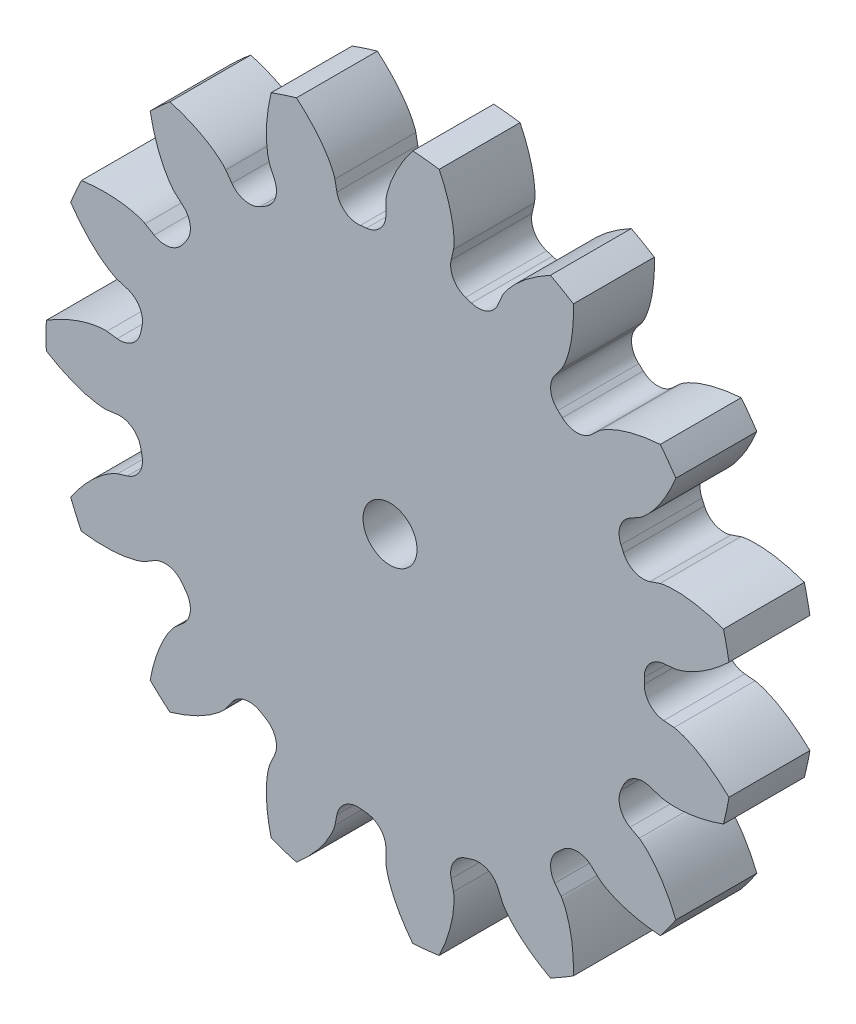
SolidWorks part; units mm, degrees
material "Acrylic (Medium-high impact)"
ref_plane "Front Plane" through (0, 0, 0) normal (0, 0, 1) x (1, 0, 0)
ref_plane "Top Plane" through (0, 0, 0) normal (0, 1, 0) x (1, 0, 0)
ref_plane "Right Plane" through (0, 0, 0) normal (1, 0, 0) x (0, 0, -1)
sketch "Model" plane through (0, 0, 0) normal (0, 0, 1) x (1, 0, 0)
  line L40 (-34.0113, -11.6188) -> (-34.7748, -11.5274)
  line L41 (-34.7748, -16.5738) -> (-34.0113, -16.4825)
  line L42 (-33.2515, -20.0567) -> (-33.9862, -20.2838)
  line L43 (-31.9337, -24.8939) -> (-31.2733, -24.4999)
  line L44 (-29.1255, -27.4561) -> (-29.7043, -27.9624)
  line L45 (-25.9541, -31.3391) -> (-25.5111, -30.7105)
  line L46 (-22.3465, -32.5376) -> (-22.6694, -33.2355)
  line L47 (-17.87, -34.7949) -> (-17.7209, -34.0405)
  line L48 (-14.0869, -34.4225) -> (-14.0979, -35.1914)
  line L49 (-9.0792, -34.6639) -> (-9.2499, -33.9141)
  line L50 (-5.7746, -32.7849) -> (-5.472, -33.4918)
  line L51 (-1.1017, -30.9686) -> (-1.5626, -30.3531)
  line L52 (1.153, -27.908) -> (1.717, -28.4307)
  line L53 (4.6832, -24.3481) -> (4.0117, -23.9732)
  line L54 (5.498, -20.635) -> (6.2259, -20.8832)
  line L55 (7.2751, -15.9471) -> (6.5092, -15.8777)
  line L56 (6.5092, -12.2236) -> (7.2751, -12.1542)
  line L57 (6.2259, -7.2181) -> (5.498, -7.4662)
  line L58 (4.0117, -4.128) -> (4.6832, -3.7532)
  line L59 (1.717, 0.3295) -> (1.153, -0.1933)
  line L60 (-1.5626, 2.2518) -> (-1.1017, 2.8674)
  line L61 (-5.472, 5.3906) -> (-5.7746, 4.6836)
  line L62 (-9.2499, 5.8128) -> (-9.0792, 6.5626)
  line L63 (-14.0979, 7.0901) -> (-14.0869, 6.3212)
  line L64 (-17.7209, 5.9392) -> (-17.87, 6.6936)
  line L65 (-22.6694, 5.1342) -> (-22.3465, 4.4363)
  line L66 (-25.5111, 2.6092) -> (-25.9541, 3.2378)
  line L67 (-29.7043, -0.1389) -> (-29.1255, -0.6452)
  line L68 (-31.2733, -3.6014) -> (-31.9337, -3.2074)
  line L69 (-33.9862, -7.8175) -> (-33.2515, -8.0446)
  arc A81 (-32.1716, -9.91) -> (-32.2659, -10.3539) centre (-13.7828, -14.0506) ccw
  arc A82 (-34.0113, -11.6188) -> (-32.2659, -10.3539) centre (-33.8226, -10.0426) ccw
  arc A83 (-39.2638, -13.0663) -> (-39.2638, -15.035) centre (-13.7828, -14.0506) ccw
  arc A84 (-32.2659, -17.7474) -> (-34.0113, -16.4825) centre (-33.8226, -18.0587) ccw
  arc A85 (-32.2659, -17.7474) -> (-32.1716, -18.1913) centre (-13.7828, -14.0506) ccw
  arc A86 (-33.2515, -20.0567) -> (-32.1716, -18.1913) centre (-33.7203, -18.54) ccw
  arc A87 (-37.4612, -23.5154) -> (-36.6605, -25.3139) centre (-13.7828, -14.0506) ccw
  arc A88 (-29.1644, -24.9455) -> (-31.2733, -24.4999) centre (-30.4599, -25.8631) ccw
  arc A89 (-29.1644, -24.9455) -> (-28.8976, -25.3127) centre (-13.7828, -14.0506) ccw
  arc A90 (-29.1255, -27.4561) -> (-28.8976, -25.3127) centre (-30.1706, -26.2612) ccw
  arc A91 (-31.5644, -32.328) -> (-30.1014, -33.6454) centre (-13.7828, -14.0506) ccw
  arc A92 (-23.4032, -30.2599) -> (-25.5111, -30.7105) centre (-24.2135, -31.625) ccw
  arc A93 (-23.4032, -30.2599) -> (-23.0102, -30.4868) centre (-13.7828, -14.0506) ccw
  arc A94 (-22.3465, -32.5376) -> (-23.0102, -30.4868) centre (-23.7874, -31.8711) ccw
  arc A95 (-22.593, -37.9803) -> (-20.7207, -38.5887) centre (-13.7828, -14.0506) ccw
  arc A96 (-15.9786, -32.7715) -> (-17.7209, -34.0405) centre (-16.1635, -34.3482) ccw
  arc A97 (-15.9786, -32.7715) -> (-15.5273, -32.8189) centre (-13.7828, -14.0506) ccw
  arc A98 (-14.0869, -34.4225) -> (-15.5273, -32.8189) centre (-15.6742, -34.3996) ccw
  arc A99 (-12.0983, -39.4949) -> (-10.1404, -39.2891) centre (-13.7828, -14.0506) ccw
  arc A100 (-8.1743, -32.0461) -> (-9.2499, -33.9141) centre (-7.702, -33.5617) ccw
  arc A101 (-8.1743, -32.0461) -> (-7.7427, -31.9059) centre (-13.7828, -14.0506) ccw
  arc A102 (-5.7746, -32.7849) -> (-7.7427, -31.9059) centre (-7.234, -33.4097) ccw
  arc A103 (-1.8948, -36.61) -> (-0.1898, -35.6257) centre (-13.7828, -14.0506) ccw
  arc A104 (-1.3398, -28.2091) -> (-1.5626, -30.3531) centre (-0.2918, -29.4016) ccw
  arc A105 (-1.3398, -28.2091) -> (-1.0025, -27.9055) centre (-13.7828, -14.0506) ccw
  arc A106 (1.153, -27.908) -> (-1.0025, -27.9055) centre (0.0739, -29.0723) ccw
  arc A107 (6.2532, -29.8243) -> (7.4103, -28.2316) centre (-13.7828, -14.0506) ccw
  arc A108 (3.3433, -21.924) -> (4.0117, -23.9732) centre (4.7856, -22.5871) ccw
  arc A109 (3.3433, -21.924) -> (3.5278, -21.5094) centre (-13.7828, -14.0506) ccw
  arc A110 (5.498, -20.635) -> (3.5278, -21.5094) centre (4.9858, -22.1376) ccw
  arc A111 (10.9367, -20.3113) -> (11.346, -18.3856) centre (-13.7828, -14.0506) ccw
  arc A112 (5.065, -14.2775) -> (6.5092, -15.8777) centre (6.6524, -14.2967) ccw
  arc A113 (5.065, -14.2775) -> (5.065, -13.8237) centre (-13.7828, -14.0506) ccw
  arc A114 (6.5092, -12.2236) -> (5.065, -13.8237) centre (6.6524, -13.8046) ccw
  arc A115 (11.346, -9.7157) -> (10.9367, -7.79) centre (-13.7828, -14.0506) ccw
  arc A116 (3.5278, -6.5918) -> (5.498, -7.4662) centre (4.9858, -5.9636) ccw
  arc A117 (3.5278, -6.5918) -> (3.3433, -6.1772) centre (-13.7828, -14.0506) ccw
  arc A118 (4.0117, -4.128) -> (3.3433, -6.1772) centre (4.7856, -5.5141) ccw
  arc A119 (7.4103, 0.1304) -> (6.2532, 1.7231) centre (-13.7828, -14.0506) ccw
  arc A120 (-1.0025, -0.1958) -> (1.153, -0.1933) centre (0.0739, 0.9711) ccw
  arc A121 (-1.0025, -0.1958) -> (-1.3398, 0.1079) centre (-13.7828, -14.0506) ccw
  arc A122 (-1.5626, 2.2518) -> (-1.3398, 0.1079) centre (-0.2918, 1.3003) ccw
  arc A123 (-0.1898, 7.5244) -> (-1.8948, 8.5087) centre (-13.7828, -14.0506) ccw
  arc A124 (-7.7427, 3.8046) -> (-5.7746, 4.6836) centre (-7.234, 5.3084) ccw
  arc A125 (-7.7427, 3.8046) -> (-8.1743, 3.9448) centre (-13.7828, -14.0506) ccw
  arc A126 (-9.2499, 5.8128) -> (-8.1743, 3.9448) centre (-7.702, 5.4604) ccw
  arc A127 (-10.1404, 11.1879) -> (-12.0983, 11.3937) centre (-13.7828, -14.0506) ccw
  arc A128 (-15.5273, 4.7177) -> (-14.0869, 6.3212) centre (-15.6742, 6.2984) ccw
  arc A129 (-15.5273, 4.7177) -> (-15.9786, 4.6702) centre (-13.7828, -14.0506) ccw
  arc A130 (-17.7209, 5.9392) -> (-15.9786, 4.6702) centre (-16.1635, 6.2469) ccw
  arc A131 (-20.7207, 10.4874) -> (-22.593, 9.8791) centre (-13.7828, -14.0506) ccw
  arc A132 (-23.0102, 2.3855) -> (-22.3465, 4.4363) centre (-23.7874, 3.7698) ccw
  arc A133 (-23.0102, 2.3855) -> (-23.4032, 2.1586) centre (-13.7828, -14.0506) ccw
  arc A134 (-25.5111, 2.6092) -> (-23.4032, 2.1586) centre (-24.2135, 3.5238) ccw
  arc A135 (-30.1014, 5.5441) -> (-31.5644, 4.2268) centre (-13.7828, -14.0506) ccw
  arc A136 (-28.8976, -2.7886) -> (-29.1255, -0.6452) centre (-30.1706, -1.8401) ccw
  arc A137 (-28.8976, -2.7886) -> (-29.1644, -3.1557) centre (-13.7828, -14.0506) ccw
  arc A138 (-31.2733, -3.6014) -> (-29.1644, -3.1557) centre (-30.4599, -2.2382) ccw
  arc A139 (-36.6605, -2.7873) -> (-37.4612, -4.5858) centre (-13.7828, -14.0506) ccw
  arc A140 (-32.1716, -9.91) -> (-33.2515, -8.0446) centre (-33.7203, -9.5613) ccw
  circle A141 centre (-13.7828, -14.0506) radius 2
  spline S40 degree 5 poles (-34.7748, -11.5274) (-34.8261, -11.5213) (-34.8905, -11.5174) (-34.981, -11.5185) (-35.0978, -11.526) (-35.2277, -11.5365) (-35.3577, -11.5484) (-35.4879, -11.5642) (-35.6442, -11.5887) (-35.8005, -11.6179) (-35.9828, -11.6559) (-36.165, -11.6984) (-36.3601, -11.7504) (-36.5549, -11.8067) (-36.8012, -11.8846) (-37.0727, -11.9796) (-37.3563, -12.0879) (-37.677, -12.2229) (-38.0088, -12.3752) (-38.3386, -12.5387) (-38.6536, -12.7065) (-38.9038, -12.8488) (-39.0904, -12.9597) (-39.2143, -13.0356) (-39.2638, -13.0663) knots 0 0 0 0 0 0 0.057143 0.071429 0.1 0.128571 0.142857 0.2 0.214286 0.271429 0.3 0.342857 0.4 0.428571 0.485714 0.571429 0.642857 0.714286 0.785714 0.857143 0.942857 1 1 1 1 1 1 weights 1 1 1 1 1 1 1 1 1 1 1 1 1 1 1 1 1 1 1 1 1 1 1 1 1
  spline S41 degree 5 poles (-39.2638, -15.035) (-39.103, -15.1346) (-38.8916, -15.2607) (-38.6287, -15.4097) (-38.3009, -15.5833) (-37.9068, -15.7736) (-37.6257, -15.9001) (-37.3177, -16.0285) (-37.0082, -16.1456) (-36.7365, -16.2385) (-36.49, -16.3143) (-36.2691, -16.3755) (-36.0869, -16.4214) (-35.9437, -16.4536) (-35.7875, -16.4856) (-35.6572, -16.5098) (-35.527, -16.531) (-35.3968, -16.5486) (-35.2667, -16.5615) (-35.1238, -16.5734) (-34.994, -16.5826) (-34.8905, -16.5839) (-34.8261, -16.58) (-34.7748, -16.5738) knots -1 -1 -1 -1 -1 -1 -0.814286 -0.757143 -0.7 -0.628571 -0.557143 -0.5 -0.414286 -0.357143 -0.328571 -0.285714 -0.257143 -0.214286 -0.2 -0.157143 -0.142857 -0.114286 -0.071429 -0.057143 0 0 0 0 0 0 weights 1 1 1 1 1 1 1 1 1 1 1 1 1 1 1 1 1 1 1 1 1 1 1 1
  spline S42 degree 5 poles (-33.9862, -20.2838) (-34.0356, -20.2991) (-34.096, -20.3217) (-34.1783, -20.3595) (-34.2819, -20.4138) (-34.3963, -20.4763) (-34.5102, -20.5401) (-34.6227, -20.6074) (-34.7555, -20.6934) (-34.8864, -20.7836) (-35.0375, -20.8925) (-35.1867, -21.0055) (-35.3438, -21.1323) (-35.4988, -21.263) (-35.6922, -21.4343) (-35.9016, -21.6315) (-36.1165, -21.8458) (-36.3547, -22.0996) (-36.5958, -22.3736) (-36.8306, -22.6571) (-37.0501, -22.9386) (-37.2208, -23.1703) (-37.3462, -23.3476) (-37.4285, -23.4673) (-37.4612, -23.5154) knots 0 0 0 0 0 0 0.057143 0.071429 0.1 0.128571 0.142857 0.2 0.214286 0.271429 0.3 0.342857 0.4 0.428571 0.485714 0.571429 0.642857 0.714286 0.785714 0.857143 0.942857 1 1 1 1 1 1 weights 1 1 1 1 1 1 1 1 1 1 1 1 1 1 1 1 1 1 1 1 1 1 1 1 1
  spline S43 degree 5 poles (-36.6605, -25.3139) (-36.473, -25.3395) (-36.2286, -25.3688) (-35.9279, -25.398) (-35.5578, -25.4232) (-35.1204, -25.4367) (-34.8121, -25.438) (-34.4785, -25.43) (-34.1482, -25.4111) (-33.8621, -25.3855) (-33.6061, -25.3545) (-33.3794, -25.3205) (-33.1944, -25.2883) (-33.0504, -25.2595) (-32.8947, -25.2252) (-32.7658, -25.1943) (-32.6382, -25.1607) (-32.5121, -25.1238) (-32.3881, -25.0827) (-32.2527, -25.0354) (-32.1303, -24.991) (-32.0353, -24.9502) (-31.9781, -24.9204) (-31.9337, -24.8939) knots -1 -1 -1 -1 -1 -1 -0.814286 -0.757143 -0.7 -0.628571 -0.557143 -0.5 -0.414286 -0.357143 -0.328571 -0.285714 -0.257143 -0.214286 -0.2 -0.157143 -0.142857 -0.114286 -0.071429 -0.057143 0 0 0 0 0 0 weights 1 1 1 1 1 1 1 1 1 1 1 1 1 1 1 1 1 1 1 1 1 1 1 1
  spline S44 degree 5 poles (-29.7043, -27.9624) (-29.7432, -27.9964) (-29.7892, -28.0417) (-29.8489, -28.1097) (-29.9215, -28.2014) (-30.0006, -28.3051) (-30.0788, -28.4096) (-30.1541, -28.5169) (-30.2405, -28.6494) (-30.3234, -28.7852) (-30.4171, -28.9461) (-30.5075, -29.1099) (-30.5994, -29.2896) (-30.6878, -29.4721) (-30.7948, -29.7073) (-30.9059, -29.9726) (-31.0151, -30.2558) (-31.1294, -30.5845) (-31.2382, -30.933) (-31.3375, -31.2874) (-31.4235, -31.6338) (-31.4852, -31.915) (-31.5276, -32.1279) (-31.5541, -32.2708) (-31.5644, -32.328) knots 0 0 0 0 0 0 0.057143 0.071429 0.1 0.128571 0.142857 0.2 0.214286 0.271429 0.3 0.342857 0.4 0.428571 0.485714 0.571429 0.642857 0.714286 0.785714 0.857143 0.942857 1 1 1 1 1 1 weights 1 1 1 1 1 1 1 1 1 1 1 1 1 1 1 1 1 1 1 1 1 1 1 1 1
  spline S45 degree 5 poles (-30.1014, -33.6454) (-29.9197, -33.5925) (-29.6846, -33.5198) (-29.398, -33.4241) (-29.0496, -33.2967) (-28.6445, -33.1311) (-28.3624, -33.0069) (-28.0608, -32.8639) (-27.7668, -32.7123) (-27.5159, -32.5725) (-27.2946, -32.4401) (-27.1013, -32.3169) (-26.9454, -32.2122) (-26.8256, -32.1273) (-26.6973, -32.0326) (-26.5921, -31.952) (-26.4892, -31.8694) (-26.389, -31.7844) (-26.2924, -31.6964) (-26.1879, -31.5981) (-26.0942, -31.5078) (-26.0241, -31.4318) (-25.9839, -31.3813) (-25.9541, -31.3391) knots -1 -1 -1 -1 -1 -1 -0.814286 -0.757143 -0.7 -0.628571 -0.557143 -0.5 -0.414286 -0.357143 -0.328571 -0.285714 -0.257143 -0.214286 -0.2 -0.157143 -0.142857 -0.114286 -0.071429 -0.057143 0 0 0 0 0 0 weights 1 1 1 1 1 1 1 1 1 1 1 1 1 1 1 1 1 1 1 1 1 1 1 1
  spline S46 degree 5 poles (-22.6694, -33.2355) (-22.6911, -33.2824) (-22.7147, -33.3424) (-22.7416, -33.4289) (-22.7706, -33.5422) (-22.8007, -33.6691) (-22.8296, -33.7964) (-22.8548, -33.925) (-22.8798, -34.0812) (-22.9003, -34.239) (-22.9205, -34.4241) (-22.9364, -34.6105) (-22.9472, -34.8121) (-22.9538, -35.0148) (-22.9559, -35.2731) (-22.9495, -35.5607) (-22.934, -35.8638) (-22.9048, -36.2106) (-22.8625, -36.5732) (-22.8089, -36.9373) (-22.7466, -37.2888) (-22.6887, -37.5707) (-22.6408, -37.7825) (-22.6069, -37.9238) (-22.593, -37.9803) knots 0 0 0 0 0 0 0.057143 0.071429 0.1 0.128571 0.142857 0.2 0.214286 0.271429 0.3 0.342857 0.4 0.428571 0.485714 0.571429 0.642857 0.714286 0.785714 0.857143 0.942857 1 1 1 1 1 1 weights 1 1 1 1 1 1 1 1 1 1 1 1 1 1 1 1 1 1 1 1 1 1 1 1 1
  spline S47 degree 5 poles (-20.7207, -38.5887) (-20.5762, -38.4665) (-20.391, -38.3044) (-20.168, -38.1005) (-19.9016, -37.8423) (-19.5989, -37.5263) (-19.3917, -37.2981) (-19.1744, -37.0448) (-18.9674, -36.7867) (-18.7951, -36.557) (-18.6468, -36.346) (-18.5203, -36.1548) (-18.4205, -35.9957) (-18.3455, -35.8695) (-18.2668, -35.7308) (-18.2035, -35.6143) (-18.1431, -35.497) (-18.0862, -35.3787) (-18.0337, -35.259) (-17.9783, -35.1267) (-17.9294, -35.0061) (-17.8962, -34.9081) (-17.88, -34.8456) (-17.87, -34.7949) knots -1 -1 -1 -1 -1 -1 -0.814286 -0.757143 -0.7 -0.628571 -0.557143 -0.5 -0.414286 -0.357143 -0.328571 -0.285714 -0.257143 -0.214286 -0.2 -0.157143 -0.142857 -0.114286 -0.071429 -0.057143 0 0 0 0 0 0 weights 1 1 1 1 1 1 1 1 1 1 1 1 1 1 1 1 1 1 1 1 1 1 1 1
  spline S48 degree 5 poles (-14.0979, -35.1914) (-14.0987, -35.2431) (-14.0958, -35.3075) (-14.0852, -35.3974) (-14.0656, -35.5128) (-14.0415, -35.6409) (-14.0161, -35.7689) (-13.9869, -35.8967) (-13.9461, -36.0496) (-13.9007, -36.202) (-13.8439, -36.3793) (-13.7826, -36.5561) (-13.7105, -36.7447) (-13.6341, -36.9325) (-13.5309, -37.1693) (-13.4081, -37.4295) (-13.2706, -37.7001) (-13.1029, -38.005) (-12.9167, -38.319) (-12.7197, -38.6299) (-12.5199, -38.9257) (-12.3522, -39.1597) (-12.2224, -39.3336) (-12.1339, -39.4489) (-12.0983, -39.4949) knots 0 0 0 0 0 0 0.057143 0.071429 0.1 0.128571 0.142857 0.2 0.214286 0.271429 0.3 0.342857 0.4 0.428571 0.485714 0.571429 0.642857 0.714286 0.785714 0.857143 0.942857 1 1 1 1 1 1 weights 1 1 1 1 1 1 1 1 1 1 1 1 1 1 1 1 1 1 1 1 1 1 1 1 1
  spline S49 degree 5 poles (-10.1404, -39.2891) (-10.0581, -39.1188) (-9.9548, -38.8954) (-9.8341, -38.6184) (-9.6957, -38.2742) (-9.5476, -37.8624) (-9.4512, -37.5696) (-9.3557, -37.2498) (-9.2716, -36.9298) (-9.2076, -36.6499) (-9.158, -36.3968) (-9.1202, -36.1707) (-9.0937, -35.9848) (-9.0765, -35.839) (-9.0611, -35.6802) (-9.0506, -35.5481) (-9.0431, -35.4164) (-9.0392, -35.2851) (-9.04, -35.1544) (-9.0432, -35.011) (-9.0476, -34.8809) (-9.0571, -34.7779) (-9.0677, -34.7143) (-9.0792, -34.6639) knots -1 -1 -1 -1 -1 -1 -0.814286 -0.757143 -0.7 -0.628571 -0.557143 -0.5 -0.414286 -0.357143 -0.328571 -0.285714 -0.257143 -0.214286 -0.2 -0.157143 -0.142857 -0.114286 -0.071429 -0.057143 0 0 0 0 0 0 weights 1 1 1 1 1 1 1 1 1 1 1 1 1 1 1 1 1 1 1 1 1 1 1 1
  spline S50 degree 5 poles (-5.472, -33.4918) (-5.4516, -33.5394) (-5.4228, -33.5971) (-5.3766, -33.6749) (-5.3117, -33.7723) (-5.2376, -33.8795) (-5.1623, -33.9862) (-5.0836, -34.091) (-4.9842, -34.2141) (-4.8808, -34.3349) (-4.7567, -34.4738) (-4.6288, -34.6103) (-4.4862, -34.7532) (-4.34, -34.8938) (-4.1495, -35.0682) (-3.9315, -35.2558) (-3.6958, -35.4472) (-3.4186, -35.6575) (-3.1208, -35.8686) (-2.8143, -36.0726) (-2.5115, -36.2614) (-2.2631, -36.407) (-2.0737, -36.5131) (-1.9461, -36.5825) (-1.8948, -36.61) knots 0 0 0 0 0 0 0.057143 0.071429 0.1 0.128571 0.142857 0.2 0.214286 0.271429 0.3 0.342857 0.4 0.428571 0.485714 0.571429 0.642857 0.714286 0.785714 0.857143 0.942857 1 1 1 1 1 1 weights 1 1 1 1 1 1 1 1 1 1 1 1 1 1 1 1 1 1 1 1 1 1 1 1 1
  spline S51 degree 5 poles (-0.1898, -35.6257) (-0.184, -35.4365) (-0.1805, -35.1904) (-0.1828, -34.8883) (-0.1964, -34.5176) (-0.2287, -34.0811) (-0.2597, -33.7745) (-0.3025, -33.4435) (-0.3558, -33.1169) (-0.4112, -32.8351) (-0.4688, -32.5838) (-0.5262, -32.3619) (-0.5776, -32.1812) (-0.6213, -32.0411) (-0.6717, -31.8897) (-0.7159, -31.7648) (-0.7626, -31.6414) (-0.8125, -31.5199) (-0.8664, -31.4008) (-0.9276, -31.2711) (-0.9845, -31.1541) (-1.0351, -31.0638) (-1.0707, -31.01) (-1.1017, -30.9686) knots -1 -1 -1 -1 -1 -1 -0.814286 -0.757143 -0.7 -0.628571 -0.557143 -0.5 -0.414286 -0.357143 -0.328571 -0.285714 -0.257143 -0.214286 -0.2 -0.157143 -0.142857 -0.114286 -0.071429 -0.057143 0 0 0 0 0 0 weights 1 1 1 1 1 1 1 1 1 1 1 1 1 1 1 1 1 1 1 1 1 1 1 1
  spline S52 degree 5 poles (1.717, -28.4307) (1.7549, -28.4659) (1.8047, -28.5069) (1.8786, -28.5592) (1.9774, -28.6218) (2.0888, -28.6896) (2.2009, -28.7564) (2.3155, -28.8201) (2.4563, -28.8922) (2.6, -28.9604) (2.7698, -29.0368) (2.9422, -29.1096) (3.1305, -29.1822) (3.3213, -29.2511) (3.5663, -29.3329) (3.8418, -29.4157) (4.1349, -29.4946) (4.4737, -29.574) (4.8316, -29.6457) (5.1945, -29.7074) (5.548, -29.7567) (5.8341, -29.7887) (6.0503, -29.8086) (6.1951, -29.8201) (6.2532, -29.8243) knots 0 0 0 0 0 0 0.057143 0.071429 0.1 0.128571 0.142857 0.2 0.214286 0.271429 0.3 0.342857 0.4 0.428571 0.485714 0.571429 0.642857 0.714286 0.785714 0.857143 0.942857 1 1 1 1 1 1 weights 1 1 1 1 1 1 1 1 1 1 1 1 1 1 1 1 1 1 1 1 1 1 1 1 1
  spline S53 degree 5 poles (7.4103, -28.2316) (7.3388, -28.0565) (7.2419, -27.8302) (7.1168, -27.5552) (6.9536, -27.222) (6.7466, -26.8365) (6.5936, -26.5689) (6.4198, -26.2839) (6.2383, -26.0073) (6.0731, -25.7724) (5.9183, -25.5662) (5.7755, -25.3868) (5.6551, -25.2427) (5.5582, -25.1324) (5.4506, -25.0147) (5.3594, -24.9185) (5.2665, -24.8248) (5.1715, -24.7341) (5.0739, -24.6472) (4.9652, -24.5536) (4.8656, -24.4699) (4.7827, -24.408) (4.7283, -24.3733) (4.6832, -24.3481) knots -1 -1 -1 -1 -1 -1 -0.814286 -0.757143 -0.7 -0.628571 -0.557143 -0.5 -0.414286 -0.357143 -0.328571 -0.285714 -0.257143 -0.214286 -0.2 -0.157143 -0.142857 -0.114286 -0.071429 -0.057143 0 0 0 0 0 0 weights 1 1 1 1 1 1 1 1 1 1 1 1 1 1 1 1 1 1 1 1 1 1 1 1
  spline S54 degree 5 poles (6.2259, -20.8832) (6.2748, -20.8999) (6.337, -20.9171) (6.4257, -20.9348) (6.5415, -20.9518) (6.6708, -20.9684) (6.8004, -20.9838) (6.931, -20.9955) (7.089, -21.004) (7.248, -21.0079) (7.4342, -21.0087) (7.6213, -21.005) (7.8228, -20.9947) (8.0251, -20.9801) (8.2822, -20.9551) (8.5676, -20.9187) (8.8675, -20.8716) (9.2093, -20.8063) (9.5654, -20.7263) (9.922, -20.635) (10.265, -20.5363) (10.5394, -20.4492) (10.745, -20.3794) (10.8819, -20.331) (10.9367, -20.3113) knots 0 0 0 0 0 0 0.057143 0.071429 0.1 0.128571 0.142857 0.2 0.214286 0.271429 0.3 0.342857 0.4 0.428571 0.485714 0.571429 0.642857 0.714286 0.785714 0.857143 0.942857 1 1 1 1 1 1 weights 1 1 1 1 1 1 1 1 1 1 1 1 1 1 1 1 1 1 1 1 1 1 1 1 1
  spline S55 degree 5 poles (11.346, -18.3856) (11.2094, -18.2547) (11.0289, -18.0874) (10.8027, -17.887) (10.5181, -17.649) (10.1722, -17.381) (9.9236, -17.1988) (9.649, -17.0092) (9.3706, -16.8303) (9.1242, -16.6829) (8.8988, -16.5575) (8.6955, -16.4517) (8.5268, -16.369) (8.3935, -16.3077) (8.2473, -16.2439) (8.1249, -16.1931) (8.0019, -16.1453) (7.8782, -16.101) (7.7537, -16.0614) (7.6163, -16.0201) (7.4913, -15.9841) (7.3903, -15.9613) (7.3266, -15.9517) (7.2751, -15.9471) knots -1 -1 -1 -1 -1 -1 -0.814286 -0.757143 -0.7 -0.628571 -0.557143 -0.5 -0.414286 -0.357143 -0.328571 -0.285714 -0.257143 -0.214286 -0.2 -0.157143 -0.142857 -0.114286 -0.071429 -0.057143 0 0 0 0 0 0 weights 1 1 1 1 1 1 1 1 1 1 1 1 1 1 1 1 1 1 1 1 1 1 1 1
  spline S56 degree 5 poles (7.2751, -12.1542) (7.3266, -12.1495) (7.3903, -12.14) (7.4786, -12.1201) (7.5913, -12.0885) (7.7162, -12.0511) (7.8409, -12.0125) (7.9649, -11.97) (8.1127, -11.9135) (8.2595, -11.8525) (8.43, -11.7774) (8.5994, -11.6979) (8.7793, -11.6065) (8.9582, -11.5109) (9.1829, -11.3836) (9.4288, -11.2342) (9.6836, -11.0692) (9.9693, -10.8705) (10.2621, -10.6526) (10.5507, -10.4241) (10.8239, -10.1945) (11.0391, -10.0033) (11.1986, -9.8559) (11.304, -9.7559) (11.346, -9.7157) knots 0 0 0 0 0 0 0.057143 0.071429 0.1 0.128571 0.142857 0.2 0.214286 0.271429 0.3 0.342857 0.4 0.428571 0.485714 0.571429 0.642857 0.714286 0.785714 0.857143 0.942857 1 1 1 1 1 1 weights 1 1 1 1 1 1 1 1 1 1 1 1 1 1 1 1 1 1 1 1 1 1 1 1 1
  spline S57 degree 5 poles (10.9367, -7.79) (10.7587, -7.726) (10.5257, -7.6466) (10.2376, -7.5555) (9.8808, -7.4538) (9.4558, -7.3497) (9.1546, -7.2844) (8.8265, -7.2228) (8.4995, -7.1726) (8.2144, -7.1382) (7.9575, -7.1153) (7.7287, -7.1014) (7.541, -7.0944) (7.3943, -7.0926) (7.2347, -7.0938) (7.1023, -7.0972) (6.9705, -7.1036) (6.8395, -7.1134) (6.7096, -7.1279) (6.5673, -7.146) (6.4384, -7.164) (6.337, -7.1842) (6.2748, -7.2014) (6.2259, -7.2181) knots -1 -1 -1 -1 -1 -1 -0.814286 -0.757143 -0.7 -0.628571 -0.557143 -0.5 -0.414286 -0.357143 -0.328571 -0.285714 -0.257143 -0.214286 -0.2 -0.157143 -0.142857 -0.114286 -0.071429 -0.057143 0 0 0 0 0 0 weights 1 1 1 1 1 1 1 1 1 1 1 1 1 1 1 1 1 1 1 1 1 1 1 1
  spline S58 degree 5 poles (4.6832, -3.7532) (4.7283, -3.728) (4.7827, -3.6933) (4.8553, -3.6391) (4.9453, -3.5645) (5.0443, -3.4796) (5.1424, -3.3935) (5.2385, -3.3043) (5.3505, -3.1926) (5.4598, -3.0771) (5.585, -2.9392) (5.7074, -2.7977) (5.8346, -2.641) (5.9591, -2.4809) (6.1126, -2.2731) (6.2765, -2.0367) (6.4422, -1.7823) (6.6223, -1.4846) (6.8012, -1.1664) (6.972, -0.8403) (7.1281, -0.5194) (7.247, -0.2572) (7.3327, -0.0577) (7.3883, 0.0765) (7.4103, 0.1304) knots 0 0 0 0 0 0 0.057143 0.071429 0.1 0.128571 0.142857 0.2 0.214286 0.271429 0.3 0.342857 0.4 0.428571 0.485714 0.571429 0.642857 0.714286 0.785714 0.857143 0.942857 1 1 1 1 1 1 weights 1 1 1 1 1 1 1 1 1 1 1 1 1 1 1 1 1 1 1 1 1 1 1 1 1
  spline S59 degree 5 poles (6.2532, 1.7231) (6.0645, 1.7091) (5.8194, 1.6869) (5.5191, 1.6529) (5.1518, 1.6007) (4.7212, 1.523) (4.4194, 1.4601) (4.0947, 1.3829) (3.7755, 1.2958) (3.5011, 1.2112) (3.2571, 1.1277) (3.0424, 1.0474) (2.8681, 0.9774) (2.7333, 0.9193) (2.5881, 0.8533) (2.4685, 0.7963) (2.3506, 0.7369) (2.235, 0.6746) (2.1222, 0.6086) (1.9996, 0.5342) (1.8891, 0.4654) (1.8047, 0.4056) (1.7549, 0.3646) (1.717, 0.3295) knots -1 -1 -1 -1 -1 -1 -0.814286 -0.757143 -0.7 -0.628571 -0.557143 -0.5 -0.414286 -0.357143 -0.328571 -0.285714 -0.257143 -0.214286 -0.2 -0.157143 -0.142857 -0.114286 -0.071429 -0.057143 0 0 0 0 0 0 weights 1 1 1 1 1 1 1 1 1 1 1 1 1 1 1 1 1 1 1 1 1 1 1 1
  spline S60 degree 5 poles (-1.1017, 2.8674) (-1.0707, 2.9088) (-1.0351, 2.9626) (-0.9908, 3.0415) (-0.9389, 3.1464) (-0.8831, 3.2642) (-0.8284, 3.3827) (-0.7769, 3.5033) (-0.72, 3.6509) (-0.6672, 3.8009) (-0.6089, 3.9778) (-0.5546, 4.1568) (-0.5021, 4.3517) (-0.4535, 4.5486) (-0.3978, 4.8008) (-0.3442, 5.0835) (-0.2963, 5.3832) (-0.2528, 5.7285) (-0.2189, 6.092) (-0.1955, 6.4593) (-0.1834, 6.816) (-0.1815, 7.1039) (-0.1843, 7.3209) (-0.188, 7.4662) (-0.1898, 7.5244) knots 0 0 0 0 0 0 0.057143 0.071429 0.1 0.128571 0.142857 0.2 0.214286 0.271429 0.3 0.342857 0.4 0.428571 0.485714 0.571429 0.642857 0.714286 0.785714 0.857143 0.942857 1 1 1 1 1 1 weights 1 1 1 1 1 1 1 1 1 1 1 1 1 1 1 1 1 1 1 1 1 1 1 1 1
  spline S61 degree 5 poles (-1.8948, 8.5087) (-2.0615, 8.4193) (-2.2764, 8.2993) (-2.5369, 8.1461) (-2.8511, 7.949) (-3.2129, 7.7028) (-3.463, 7.5227) (-3.7283, 7.3201) (-3.9844, 7.1107) (-4.2008, 6.9218) (-4.3896, 6.7462) (-4.5531, 6.5855) (-4.6838, 6.4507) (-4.7834, 6.3428) (-4.8892, 6.2234) (-4.9753, 6.1227) (-5.0588, 6.0206) (-5.1391, 5.9166) (-5.2153, 5.8104) (-5.2971, 5.6925) (-5.37, 5.5847) (-5.4228, 5.4958) (-5.4516, 5.4381) (-5.472, 5.3906) knots -1 -1 -1 -1 -1 -1 -0.814286 -0.757143 -0.7 -0.628571 -0.557143 -0.5 -0.414286 -0.357143 -0.328571 -0.285714 -0.257143 -0.214286 -0.2 -0.157143 -0.142857 -0.114286 -0.071429 -0.057143 0 0 0 0 0 0 weights 1 1 1 1 1 1 1 1 1 1 1 1 1 1 1 1 1 1 1 1 1 1 1 1
  spline S62 degree 5 poles (-9.0792, 6.5626) (-9.0677, 6.613) (-9.0571, 6.6767) (-9.0487, 6.7668) (-9.0439, 6.8837) (-9.0409, 7.014) (-9.0391, 7.1446) (-9.0412, 7.2756) (-9.0492, 7.4336) (-9.0619, 7.5922) (-9.0807, 7.7774) (-9.1039, 7.9631) (-9.1352, 8.1625) (-9.1709, 8.3621) (-9.2225, 8.6152) (-9.2886, 8.8952) (-9.3668, 9.1885) (-9.4675, 9.5216) (-9.5843, 9.8675) (-9.7123, 10.2126) (-9.8463, 10.5434) (-9.9617, 10.8071) (-10.0525, 11.0043) (-10.115, 11.1355) (-10.1404, 11.1879) knots 0 0 0 0 0 0 0.057143 0.071429 0.1 0.128571 0.142857 0.2 0.214286 0.271429 0.3 0.342857 0.4 0.428571 0.485714 0.571429 0.642857 0.714286 0.785714 0.857143 0.942857 1 1 1 1 1 1 weights 1 1 1 1 1 1 1 1 1 1 1 1 1 1 1 1 1 1 1 1 1 1 1 1 1
  spline S63 degree 5 poles (-12.0983, 11.3937) (-12.2142, 11.2441) (-12.3617, 11.0471) (-12.5373, 10.8012) (-12.7443, 10.4933) (-12.9747, 10.1213) (-13.1299, 9.855) (-13.2898, 9.562) (-13.4386, 9.2665) (-13.5594, 9.006) (-13.6605, 8.7688) (-13.7445, 8.5555) (-13.8091, 8.3791) (-13.8562, 8.2401) (-13.9043, 8.088) (-13.942, 7.961) (-13.9767, 7.8337) (-14.0078, 7.706) (-14.0342, 7.578) (-14.061, 7.4371) (-14.0837, 7.309) (-14.0958, 7.2062) (-14.0987, 7.1418) (-14.0979, 7.0901) knots -1 -1 -1 -1 -1 -1 -0.814286 -0.757143 -0.7 -0.628571 -0.557143 -0.5 -0.414286 -0.357143 -0.328571 -0.285714 -0.257143 -0.214286 -0.2 -0.157143 -0.142857 -0.114286 -0.071429 -0.057143 0 0 0 0 0 0 weights 1 1 1 1 1 1 1 1 1 1 1 1 1 1 1 1 1 1 1 1 1 1 1 1
  spline S64 degree 5 poles (-17.87, 6.6936) (-17.88, 6.7444) (-17.8962, 6.8068) (-17.9252, 6.8925) (-17.9684, 7.0013) (-18.0186, 7.1216) (-18.0701, 7.2416) (-18.1253, 7.3605) (-18.1969, 7.5015) (-18.273, 7.6412) (-18.3655, 7.8028) (-18.4622, 7.963) (-18.5719, 8.1324) (-18.6857, 8.3003) (-18.8358, 8.5105) (-19.0101, 8.7394) (-19.2008, 8.9756) (-19.4282, 9.2389) (-19.6756, 9.5074) (-19.933, 9.7705) (-20.19, 10.0182) (-20.4026, 10.2123) (-20.5658, 10.3554) (-20.6763, 10.4498) (-20.7207, 10.4874) knots 0 0 0 0 0 0 0.057143 0.071429 0.1 0.128571 0.142857 0.2 0.214286 0.271429 0.3 0.342857 0.4 0.428571 0.485714 0.571429 0.642857 0.714286 0.785714 0.857143 0.942857 1 1 1 1 1 1 weights 1 1 1 1 1 1 1 1 1 1 1 1 1 1 1 1 1 1 1 1 1 1 1 1 1
  spline S65 degree 5 poles (-22.593, 9.8791) (-22.6381, 9.6953) (-22.6927, 9.4553) (-22.7532, 9.1592) (-22.817, 8.7938) (-22.8762, 8.3602) (-22.9096, 8.0538) (-22.9365, 7.7211) (-22.9523, 7.3907) (-22.9567, 7.1035) (-22.9526, 6.8457) (-22.9426, 6.6166) (-22.9299, 6.4293) (-22.9163, 6.2831) (-22.8984, 6.1246) (-22.8812, 5.9932) (-22.8611, 5.8628) (-22.8376, 5.7336) (-22.8097, 5.6059) (-22.7768, 5.4663) (-22.7454, 5.34) (-22.7147, 5.2412) (-22.6911, 5.1812) (-22.6694, 5.1342) knots -1 -1 -1 -1 -1 -1 -0.814286 -0.757143 -0.7 -0.628571 -0.557143 -0.5 -0.414286 -0.357143 -0.328571 -0.285714 -0.257143 -0.214286 -0.2 -0.157143 -0.142857 -0.114286 -0.071429 -0.057143 0 0 0 0 0 0 weights 1 1 1 1 1 1 1 1 1 1 1 1 1 1 1 1 1 1 1 1 1 1 1 1
  spline S66 degree 5 poles (-25.9541, 3.2378) (-25.9839, 3.2801) (-26.0241, 3.3305) (-26.0855, 3.397) (-26.1691, 3.4788) (-26.2639, 3.5683) (-26.3598, 3.657) (-26.4585, 3.7431) (-26.5813, 3.8429) (-26.7076, 3.9395) (-26.8579, 4.0496) (-27.0114, 4.1565) (-27.1805, 4.2667) (-27.3528, 4.3738) (-27.5754, 4.5047) (-27.8277, 4.643) (-28.098, 4.7812) (-28.4129, 4.9292) (-28.7481, 5.0738) (-29.0902, 5.2096) (-29.4257, 5.3313) (-29.6989, 5.4221) (-29.9062, 5.4865) (-30.0455, 5.5278) (-30.1014, 5.5441) knots 0 0 0 0 0 0 0.057143 0.071429 0.1 0.128571 0.142857 0.2 0.214286 0.271429 0.3 0.342857 0.4 0.428571 0.485714 0.571429 0.642857 0.714286 0.785714 0.857143 0.942857 1 1 1 1 1 1 weights 1 1 1 1 1 1 1 1 1 1 1 1 1 1 1 1 1 1 1 1 1 1 1 1 1
  spline S67 degree 5 poles (-31.5644, 4.2268) (-31.5309, 4.0406) (-31.4831, 3.7991) (-31.418, 3.5041) (-31.3276, 3.1443) (-31.2053, 2.7241) (-31.1112, 2.4306) (-31.0005, 2.1157) (-30.8805, 1.8074) (-30.7677, 1.5433) (-30.6591, 1.3094) (-30.5568, 1.1043) (-30.469, 0.9382) (-30.3971, 0.8102) (-30.3163, 0.6727) (-30.2472, 0.5597) (-30.1758, 0.4487) (-30.1017, 0.3402) (-30.0243, 0.2349) (-29.9375, 0.1207) (-29.8574, 0.0181) (-29.7892, -0.0596) (-29.7432, -0.1049) (-29.7043, -0.1389) knots -1 -1 -1 -1 -1 -1 -0.814286 -0.757143 -0.7 -0.628571 -0.557143 -0.5 -0.414286 -0.357143 -0.328571 -0.285714 -0.257143 -0.214286 -0.2 -0.157143 -0.142857 -0.114286 -0.071429 -0.057143 0 0 0 0 0 0 weights 1 1 1 1 1 1 1 1 1 1 1 1 1 1 1 1 1 1 1 1 1 1 1 1
  spline S68 degree 5 poles (-31.9337, -3.2074) (-31.9781, -3.1809) (-32.0353, -3.1511) (-32.1185, -3.1153) (-32.2281, -3.0746) (-32.3511, -3.0315) (-32.4748, -2.9894) (-32.6, -2.9509) (-32.7528, -2.9097) (-32.9075, -2.8728) (-33.0895, -2.8334) (-33.2733, -2.7981) (-33.4726, -2.7662) (-33.6735, -2.7385) (-33.9301, -2.7094) (-34.2168, -2.6857) (-34.5199, -2.6694) (-34.8678, -2.6623) (-35.2329, -2.6665) (-35.6007, -2.6816) (-35.9567, -2.7069) (-36.2432, -2.735) (-36.4587, -2.7605) (-36.6028, -2.7795) (-36.6605, -2.7873) knots 0 0 0 0 0 0 0.057143 0.071429 0.1 0.128571 0.142857 0.2 0.214286 0.271429 0.3 0.342857 0.4 0.428571 0.485714 0.571429 0.642857 0.714286 0.785714 0.857143 0.942857 1 1 1 1 1 1 weights 1 1 1 1 1 1 1 1 1 1 1 1 1 1 1 1 1 1 1 1 1 1 1 1 1
  spline S69 degree 5 poles (-37.4612, -4.5858) (-37.3548, -4.7423) (-37.213, -4.9434) (-37.0335, -5.1865) (-36.8046, -5.4784) (-36.522, -5.8125) (-36.3166, -6.0424) (-36.0874, -6.285) (-35.8524, -6.5179) (-35.6419, -6.7133) (-35.4476, -6.8828) (-35.2707, -7.0286) (-35.1229, -7.1445) (-35.0052, -7.2322) (-34.8755, -7.325) (-34.7663, -7.4001) (-34.6559, -7.4725) (-34.5442, -7.5415) (-34.4306, -7.6061) (-34.3048, -7.6751) (-34.19, -7.7363) (-34.096, -7.7796) (-34.0356, -7.8022) (-33.9862, -7.8175) knots -1 -1 -1 -1 -1 -1 -0.814286 -0.757143 -0.7 -0.628571 -0.557143 -0.5 -0.414286 -0.357143 -0.328571 -0.285714 -0.257143 -0.214286 -0.2 -0.157143 -0.142857 -0.114286 -0.071429 -0.057143 0 0 0 0 0 0 weights 1 1 1 1 1 1 1 1 1 1 1 1 1 1 1 1 1 1 1 1 1 1 1 1
extrude "Boss-Extrude3" add sketch "Model" along normal blind 6
sketch "Sketch2" plane through (0, 0, 6) normal (0, 0, 1) x (1, 0, 0)
  circle A0 centre (-13.7828, -14.0506) radius 22.5
  dimension "D1" = 45
